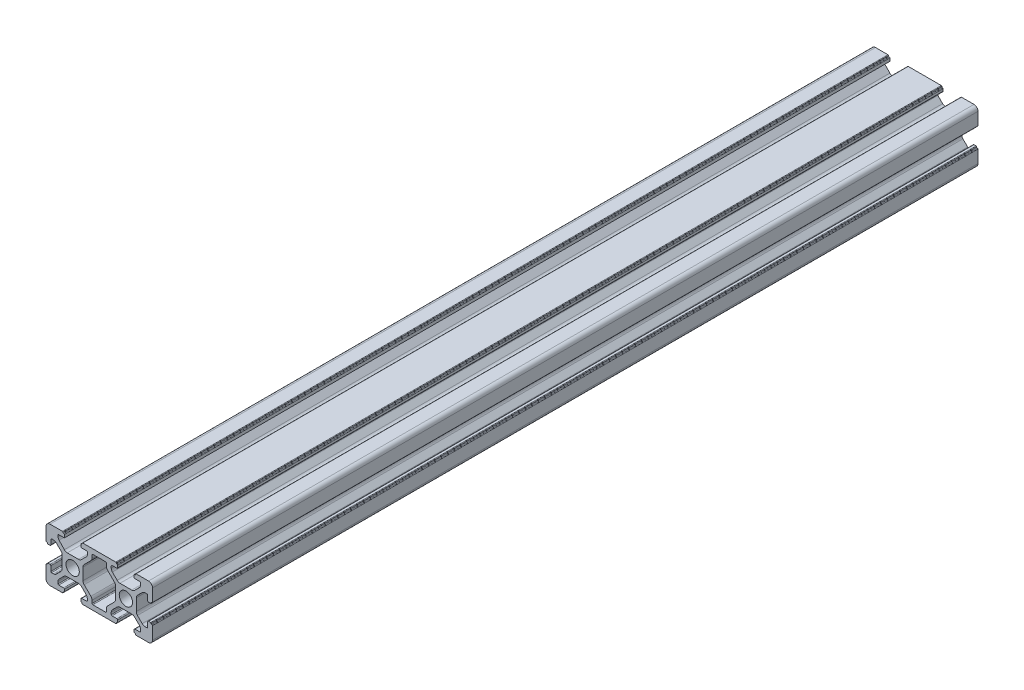
SolidWorks part; units mm, degrees
material "6063-O"
ref_plane "Front Plane" through (0, 0, 0) normal (0, 0, 1) x (1, 0, 0)
ref_plane "Top Plane" through (0, 0, 0) normal (0, 1, 0) x (1, 0, 0)
ref_plane "Right Plane" through (0, 0, 0) normal (1, 0, 0) x (0, 0, -1)
sketch "Sketch1" plane through (0, 0, 0) normal (0, 0, 1) x (1, 0, 0)
  line L0 (1.5, 0) -> (6.2, 0)
  line L1 (40, 1.5) -> (40, 6.2)
  line L2 (38.5, 20) -> (33.8, 20)
  line L3 (0, 18.5) -> (0, 13.8)
  line L4 (17.6, 1.8) -> (22.4, 1.8)
  line L5 (32.218, 13.9) -> (27.782, 13.9)
  line L6 (26.1, 12.218) -> (26.1, 7.782)
  line L7 (17.6, 18.2) -> (22.4, 18.2)
  line L8 (12.218, 13.9) -> (7.9864, 13.9)
  line L9 (6.1, 12.218) -> (6.1, 7.782)
  line L10 (7.782, 6.1) -> (12.218, 6.1)
  line L11 (13.9, 7.782) -> (13.9, 12.218)
  line L12 (27.782, 6.1) -> (32.218, 6.1)
  line L13 (33.9, 7.782) -> (33.9, 12.218)
  line L14 (26.7213, 14.3393) -> (24.9393, 16.1213)
  line L15 (33.2787, 14.3393) -> (35.0607, 16.1213)
  line L16 (34.3393, 13.2787) -> (36.1213, 15.0607)
  line L17 (25.6607, 6.7213) -> (23.1393, 4.2)
  line L18 (15.2, 1.8) -> (13.4, 1.8)
  line L19 (26.7213, 5.6607) -> (24.9393, 3.8787)
  line L20 (24.8, 1.8) -> (26.6, 1.8)
  line L21 (15.3, 18.2) -> (13.1, 18.2)
  line L22 (13.2787, 14.3393) -> (15.1607, 16.2213)
  line L23 (14.3393, 13.2787) -> (16.8607, 15.8)
  line L24 (5.6607, 6.7213) -> (3.8787, 4.9393)
  line L25 (6.7213, 5.6607) -> (4.9393, 3.8787)
  line L26 (6.897, 14.3689) -> (4.9106, 16.4674)
  line L27 (5.6607, 13.2787) -> (3.8787, 15.0607)
  line L28 (14.3393, 6.7213) -> (16.8607, 4.2)
  line L29 (13.2787, 5.6607) -> (15.0607, 3.8787)
  line L30 (24.8, 18.2) -> (26.6, 18.2)
  line L31 (25.6607, 13.2787) -> (23.1393, 15.8)
  line L32 (34.3393, 6.7213) -> (36.1213, 4.9393)
  line L33 (33.2787, 5.6607) -> (35.0607, 3.8787)
  line L34 (1.8, 15.2) -> (1.8, 13.4)
  line L35 (24.5, 2.1) -> (24.5, 2.818)
  line L36 (4.5, 2.1) -> (4.5, 2.818)
  line L37 (2.818, 4.5) -> (2.1, 4.5)
  line L38 (4.5, 17.9) -> (4.5, 17.4986)
  line L39 (2.818, 15.5) -> (2.1, 15.5)
  line L40 (15.6, 17.9) -> (15.6, 17.282)
  line L41 (15.5, 2.818) -> (15.5, 2.1)
  line L42 (38.2, 15.2) -> (38.2, 13.4)
  line L43 (35.5, 2.818) -> (35.5, 2.1)
  line L44 (37.182, 4.5) -> (37.9, 4.5)
  line L45 (35.5, 17.182) -> (35.5, 17.9)
  line L46 (37.182, 15.5) -> (37.9, 15.5)
  line L47 (17.3, 2.1) -> (17.3, 3.1393)
  line L48 (22.7, 2.1) -> (22.7, 3.1393)
  line L49 (17.3, 17.9) -> (17.3, 16.8607)
  line L50 (22.7, 17.9) -> (22.7, 16.8607)
  line L51 (24.5, 17.9) -> (24.5, 17.182)
  line L52 (6.9, 19.3) -> (6.9, 18.2)
  line L53 (13.1, 19.3) -> (13.1, 18.2)
  line L54 (6.9, 1.5) -> (6.9, 0.7)
  line L55 (13.1, 1.5) -> (13.1, 0.7)
  line L56 (13.8, 0) -> (26.2, 0)
  line L57 (6.6, 1.8) -> (4.8, 1.8)
  line L58 (6.9, 18.2) -> (4.8, 18.2)
  line L59 (6.2, 20) -> (1.5, 20)
  line L60 (39.3, 6.9) -> (38.5, 6.9)
  line L61 (39.3, 13.1) -> (38.5, 13.1)
  line L62 (1.5, 13.1) -> (0.7, 13.1)
  line L63 (1.5, 6.9) -> (0.7, 6.9)
  line L64 (0, 6.2) -> (0, 1.5)
  line L65 (1.8, 6.6) -> (1.8, 4.8)
  line L66 (38.2, 6.6) -> (38.2, 4.8)
  line L67 (40, 13.8) -> (40, 18.5)
  line L68 (33.1, 19.3) -> (33.1, 18.5)
  line L69 (26.9, 19.3) -> (26.9, 18.5)
  line L70 (26.9, 1.5) -> (26.9, 0.7)
  line L71 (33.1, 1.5) -> (33.1, 0.7)
  line L72 (33.8, 0) -> (38.5, 0)
  line L73 (33.4, 1.8) -> (35.2, 1.8)
  line L74 (26.2, 20) -> (13.8, 20)
  line L75 (33.4, 18.2) -> (35.2, 18.2)
  line L76 (6.7, 0.5) -> (6.6, 0.5)
  line L77 (6.4, 0.3) -> (6.4, 0.2)
  line L78 (13.3, 0.5) -> (13.4, 0.5)
  line L79 (13.6, 0.3) -> (13.6, 0.2)
  line L80 (26.7, 0.5) -> (26.6, 0.5)
  line L81 (26.4, 0.3) -> (26.4, 0.2)
  line L82 (33.3, 0.5) -> (33.4, 0.5)
  line L83 (33.6, 0.3) -> (33.6, 0.2)
  line L85 (6.4, 19.8) -> (6.4, 19.7)
  line L86 (6.6, 19.5) -> (6.7, 19.5)
  line L87 (13.6, 19.8) -> (13.6, 19.7)
  line L88 (13.4, 19.5) -> (13.3, 19.5)
  line L89 (26.4, 19.8) -> (26.4, 19.7)
  line L90 (26.6, 19.5) -> (26.7, 19.5)
  line L91 (33.6, 19.8) -> (33.6, 19.7)
  line L92 (33.4, 19.5) -> (33.3, 19.5)
  line L93 (0.5, 13.3) -> (0.5, 13.4)
  line L94 (0.3, 13.6) -> (0.2, 13.6)
  line L95 (0.5, 6.7) -> (0.5, 6.6)
  line L96 (0.3, 6.4) -> (0.2, 6.4)
  line L97 (39.5, 13.3) -> (39.5, 13.4)
  line L98 (39.7, 13.6) -> (39.8, 13.6)
  line L99 (39.5, 6.7) -> (39.5, 6.6)
  line L100 (39.7, 6.4) -> (39.8, 6.4)
  circle A0 centre (10, 10) radius 2.5
  circle A1 centre (30, 10) radius 2.5
  arc A2 (38.5, 0) -> (40, 1.5) centre (38.5, 1.5) ccw
  arc A3 (40, 18.5) -> (38.5, 20) centre (38.5, 18.5) ccw
  arc A4 (1.5, 0) -> (0, 1.5) centre (1.5, 1.5) cw
  arc A5 (1.5, 20) -> (0, 18.5) centre (1.5, 18.5) ccw
  arc A6 (26.7213, 5.6607) -> (27.782, 6.1) centre (27.782, 4.6) cw
  arc A7 (32.218, 6.1) -> (33.2787, 5.6607) centre (32.218, 4.6) cw
  arc A8 (33.9, 7.782) -> (34.3393, 6.7213) centre (35.4, 7.782) ccw
  arc A9 (33.2787, 14.3393) -> (32.218, 13.9) centre (32.218, 15.4) cw
  arc A10 (14.3393, 6.7213) -> (13.9, 7.782) centre (15.4, 7.782) cw
  arc A11 (14.3393, 13.2787) -> (13.9, 12.218) centre (15.4, 12.218) ccw
  arc A12 (25.6607, 6.7213) -> (26.1, 7.782) centre (24.6, 7.782) ccw
  arc A13 (26.1, 12.218) -> (25.6607, 13.2787) centre (24.6, 12.218) ccw
  arc A14 (27.782, 13.9) -> (26.7213, 14.3393) centre (27.782, 15.4) cw
  arc A15 (5.6607, 13.2787) -> (6.1, 12.218) centre (4.6, 12.218) cw
  arc A16 (5.6607, 6.7213) -> (6.1, 7.782) centre (4.6, 7.782) ccw
  arc A17 (13.2787, 5.6607) -> (12.218, 6.1) centre (12.218, 4.6) ccw
  arc A18 (6.7213, 5.6607) -> (7.782, 6.1) centre (7.782, 4.6) cw
  arc A19 (13.2787, 14.3393) -> (12.218, 13.9) centre (12.218, 15.4) cw
  arc A20 (6.897, 14.3689) -> (7.9864, 13.9) centre (7.9864, 15.4) ccw
  arc A21 (36.1213, 4.9393) -> (37.182, 4.5) centre (37.182, 6) ccw
  arc A22 (36.1213, 15.0607) -> (37.182, 15.5) centre (37.182, 14) cw
  arc A23 (35.0607, 16.1213) -> (35.5, 17.182) centre (34, 17.182) ccw
  arc A24 (24.5, 17.182) -> (24.9393, 16.1213) centre (26, 17.182) ccw
  arc A25 (22.7, 16.8607) -> (23.1393, 15.8) centre (24.2, 16.8607) ccw
  arc A26 (17.3, 16.8607) -> (16.8607, 15.8) centre (15.8, 16.8607) cw
  arc A27 (4.9106, 16.4674) -> (4.5, 17.4986) centre (6, 17.4986) cw
  arc A28 (15.6, 17.282) -> (15.1607, 16.2213) centre (14.1, 17.282) cw
  arc A29 (3.8787, 15.0607) -> (2.818, 15.5) centre (2.818, 14) ccw
  arc A30 (3.8787, 4.9393) -> (2.818, 4.5) centre (2.818, 6) cw
  arc A31 (4.9393, 3.8787) -> (4.5, 2.818) centre (6, 2.818) ccw
  arc A32 (35.0607, 3.8787) -> (35.5, 2.818) centre (34, 2.818) cw
  arc A33 (24.9393, 3.8787) -> (24.5, 2.818) centre (26, 2.818) ccw
  arc A34 (22.7, 3.1393) -> (23.1393, 4.2) centre (24.2, 3.1393) cw
  arc A35 (17.3, 3.1393) -> (16.8607, 4.2) centre (15.8, 3.1393) ccw
  arc A36 (15.5, 2.818) -> (15.0607, 3.8787) centre (14, 2.818) ccw
  arc A37 (1.8, 6.6) -> (1.5, 6.9) centre (1.5, 6.6) ccw
  arc A38 (1.8, 13.4) -> (1.5, 13.1) centre (1.5, 13.4) cw
  arc A39 (17.6, 18.2) -> (17.3, 17.9) centre (17.6, 17.9) ccw
  arc A40 (22.4, 1.8) -> (22.7, 2.1) centre (22.4, 2.1) ccw
  arc A41 (17.6, 1.8) -> (17.3, 2.1) centre (17.6, 2.1) cw
  arc A42 (15.2, 1.8) -> (15.5, 2.1) centre (15.2, 2.1) ccw
  arc A43 (6.6, 1.8) -> (6.9, 1.5) centre (6.6, 1.5) cw
  arc A44 (13.4, 1.8) -> (13.1, 1.5) centre (13.4, 1.5) ccw
  arc A45 (24.8, 1.8) -> (24.5, 2.1) centre (24.8, 2.1) cw
  arc A46 (35.2, 1.8) -> (35.5, 2.1) centre (35.2, 2.1) ccw
  arc A47 (26.6, 1.8) -> (26.9, 1.5) centre (26.6, 1.5) cw
  arc A48 (33.4, 1.8) -> (33.1, 1.5) centre (33.4, 1.5) ccw
  arc A49 (26.9, 18.5) -> (26.6, 18.2) centre (26.6, 18.5) cw
  arc A50 (33.1, 18.5) -> (33.4, 18.2) centre (33.4, 18.5) ccw
  arc A51 (37.9, 4.5) -> (38.2, 4.8) centre (37.9, 4.8) ccw
  arc A52 (38.5, 13.1) -> (38.2, 13.4) centre (38.5, 13.4) cw
  arc A53 (38.5, 6.9) -> (38.2, 6.6) centre (38.5, 6.6) ccw
  arc A54 (38.2, 15.2) -> (37.9, 15.5) centre (37.9, 15.2) ccw
  arc A55 (35.2, 18.2) -> (35.5, 17.9) centre (35.2, 17.9) cw
  arc A56 (24.8, 18.2) -> (24.5, 17.9) centre (24.8, 17.9) ccw
  arc A57 (22.4, 18.2) -> (22.7, 17.9) centre (22.4, 17.9) cw
  arc A58 (15.3, 18.2) -> (15.6, 17.9) centre (15.3, 17.9) cw
  arc A59 (4.5, 17.9) -> (4.8, 18.2) centre (4.8, 17.9) cw
  arc A60 (1.8, 15.2) -> (2.1, 15.5) centre (2.1, 15.2) cw
  arc A61 (1.8, 4.8) -> (2.1, 4.5) centre (2.1, 4.8) ccw
  arc A62 (4.5, 2.1) -> (4.8, 1.8) centre (4.8, 2.1) ccw
  arc A63 (34.3393, 13.2787) -> (33.9, 12.218) centre (35.4, 12.218) ccw
  arc A64 (6.4, 0.2) -> (6.2, 0) centre (6.2, 0.2) cw
  arc A65 (6.6, 0.5) -> (6.4, 0.3) centre (6.6, 0.3) ccw
  arc A66 (6.7, 0.5) -> (6.9, 0.7) centre (6.7, 0.7) ccw
  arc A67 (13.6, 0.2) -> (13.8, 0) centre (13.8, 0.2) ccw
  arc A68 (13.4, 0.5) -> (13.6, 0.3) centre (13.4, 0.3) cw
  arc A69 (13.3, 0.5) -> (13.1, 0.7) centre (13.3, 0.7) cw
  arc A70 (26.4, 0.2) -> (26.2, 0) centre (26.2, 0.2) cw
  arc A71 (26.6, 0.5) -> (26.4, 0.3) centre (26.6, 0.3) ccw
  arc A72 (26.7, 0.5) -> (26.9, 0.7) centre (26.7, 0.7) ccw
  arc A73 (33.6, 0.2) -> (33.8, 0) centre (33.8, 0.2) ccw
  arc A74 (33.4, 0.5) -> (33.6, 0.3) centre (33.4, 0.3) cw
  arc A75 (33.3, 0.5) -> (33.1, 0.7) centre (33.3, 0.7) cw
  arc A76 (39.8, 6.4) -> (40, 6.2) centre (39.8, 6.2) cw
  arc A77 (39.5, 6.6) -> (39.7, 6.4) centre (39.7, 6.6) ccw
  arc A78 (39.5, 6.7) -> (39.3, 6.9) centre (39.3, 6.7) ccw
  arc A79 (39.5, 13.3) -> (39.3, 13.1) centre (39.3, 13.3) cw
  arc A80 (39.5, 13.4) -> (39.7, 13.6) centre (39.7, 13.4) cw
  arc A81 (39.8, 13.6) -> (40, 13.8) centre (39.8, 13.8) ccw
  arc A82 (33.3, 19.5) -> (33.1, 19.3) centre (33.3, 19.3) ccw
  arc A83 (33.6, 19.7) -> (33.4, 19.5) centre (33.4, 19.7) cw
  arc A84 (33.6, 19.8) -> (33.8, 20) centre (33.8, 19.8) cw
  arc A85 (26.7, 19.5) -> (26.9, 19.3) centre (26.7, 19.3) cw
  arc A86 (26.4, 19.7) -> (26.6, 19.5) centre (26.6, 19.7) ccw
  arc A87 (26.4, 19.8) -> (26.2, 20) centre (26.2, 19.8) ccw
  arc A88 (0.2, 6.4) -> (0, 6.2) centre (0.2, 6.2) ccw
  arc A89 (0.5, 6.6) -> (0.3, 6.4) centre (0.3, 6.6) cw
  arc A90 (0.5, 6.7) -> (0.7, 6.9) centre (0.7, 6.7) cw
  arc A91 (13.3, 19.5) -> (13.1, 19.3) centre (13.3, 19.3) ccw
  arc A92 (13.6, 19.7) -> (13.4, 19.5) centre (13.4, 19.7) cw
  arc A93 (13.6, 19.8) -> (13.8, 20) centre (13.8, 19.8) cw
  arc A94 (6.2, 20) -> (6.4, 19.8) centre (6.2, 19.8) cw
  arc A95 (6.7, 19.5) -> (6.9, 19.3) centre (6.7, 19.3) cw
  arc A96 (6.4, 19.7) -> (6.6, 19.5) centre (6.6, 19.7) ccw
  arc A97 (0.5, 13.3) -> (0.7, 13.1) centre (0.7, 13.3) ccw
  arc A98 (0.2, 13.6) -> (0, 13.8) centre (0.2, 13.8) cw
  arc A99 (0.5, 13.4) -> (0.3, 13.6) centre (0.3, 13.4) ccw
  point P87 (0, 0)
  point P178 (1.8, 6.9)
  point P181 (1.8, 13.1)
  point P186 (22.7, 1.8)
  point P193 (6.9, 1.8)
  point P204 (33.1, 1.8)
  point P209 (33.1, 18.2)
  point P216 (38.2, 6.9)
  point P243 (6.9, 0.5)
  point P248 (13.6, 0.5)
  point P257 (26.9, 0.5)
extrude "Boss-Extrude2" add sketch "Sketch1" along normal blind 330 contours A57 L7 A39 L49 A26 L23 A11 L11 A10 L28 A35 L47 A41 L4 A40 L48 A34 L17 A12 L6 A13 L31 A25 L50 | A0 | A1 | L59 A5 L3 A98 L94 A99 L93 A97 L62 A38 L34 A60 L39 A29 L27 A15 L9 A16 L24 A30 L37 A61 L65 A37 L63 A90 L95 A89 L96 A88 L64 A4 L0 A64 L77 A65 L76 A66 L54 A43 L57 A62 L36 A31 L25 A18 L10 A17 L29 A36 L41 A42 L18 A44 L55 A69 L78 A68 L79 A67 L56 A70 L81 A71 L80 A72 L70 A47 L20 A45 L35 A33 L19 A6 L12 A7 L33 A32 L43 A46 L73 A48 L71 A75 L82 A74 L83 A73 L72 A2 L1 A76 L100 A77 L99 A78 L60 A53 L66 A51 L44 A21 L32 A8 L13 A63 L16 A22 L46 A54 L42 A52 L61 A79 L97 A80 L98 A81 L67 A3 L2 A84 L91 A83 L92 A82 L68 A50 L75 A55 L45 A23 L15 A9 L5 A14 L14 A24 L51 A56 L30 A49 L69 A85 L90 A86 L89 A87 L74 A93 L87 A92 L88 A91 L53 L21 A58 L40 A28 L22 A19 L8 A20 L26 A27 L38 A59 L58 L52 A95 L86 A96 L85 A94
sketch "Croquis1" plane through (0, 0, 0) normal (0, 0, -1) x (-1, 0, 0)
  line L1 (-58.8417, 36.7734) -> (17.1483, 36.7734)
  line L2 (-58.8417, 36.7734) -> (-58.8417, -16.1086)
  line L3 (-58.8417, -16.1086) -> (17.1483, -16.1086)
  line L4 (17.1483, 36.7734) -> (17.1483, -16.1086)
  line L5 (-58.8417, 36.7734) -> (17.1483, -16.1086) construction
  line L6 (-58.8417, -16.1086) -> (17.1483, 36.7734) construction
  point P0 (-20.8467, 10.3324)
extrude "Cortar-Extruir1" cut sketch "Croquis1" against normal blind 20
